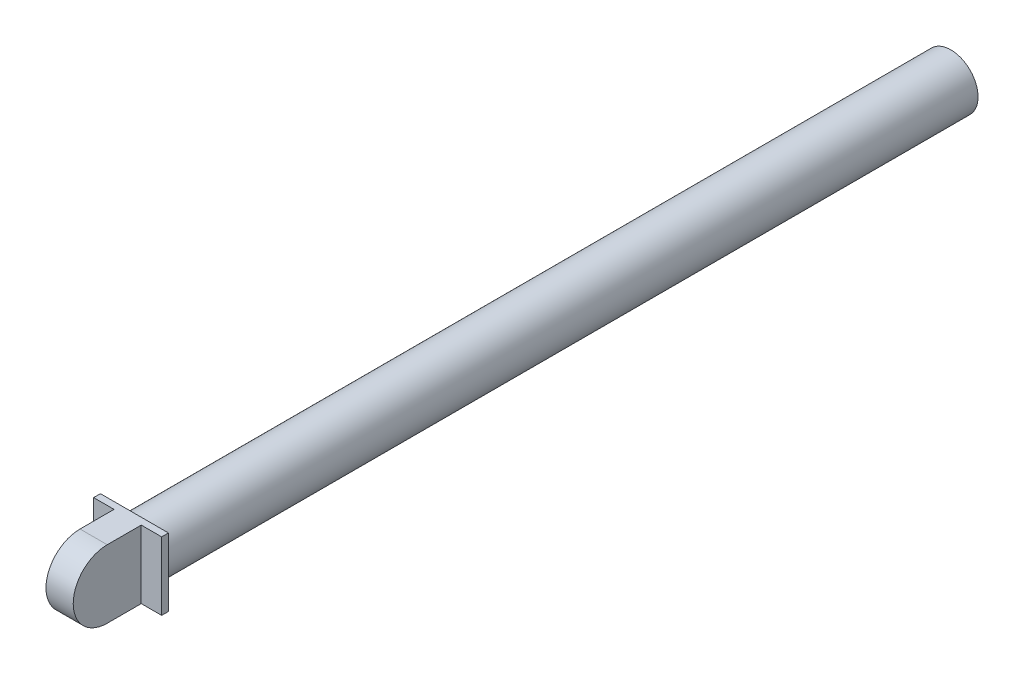
SolidWorks part; units mm, degrees
ref_plane "Front" through (0, 0, 0) normal (0, 0, 1) x (1, 0, 0)
ref_plane "Top" through (0, 0, 0) normal (0, 1, 0) x (1, 0, 0)
ref_plane "Right" through (0, 0, 0) normal (1, 0, 0) x (0, 0, -1)
sketch "草图1" plane through (0, 0, 0) normal (0, 0, 1) x (1, 0, 0)
  line L1 (-5, 5) -> (5, 5)
  line L2 (-5, 5) -> (-5, -5)
  line L3 (-5, -5) -> (5, -5)
  line L4 (5, 5) -> (5, -5)
  dimension "D1" = 10
  dimension "D2" = 10
  dimension "D3" = 5
  dimension "D4" = 5
extrude "凸台-拉伸1" add sketch "草图1" along normal blind 11
sketch "草图2" plane through (0, 5, 0) normal (0, 1, 0) x (1, 0, 0)
  line L0 (5, -11) -> (-5, -11) construction
  line L2 (-2, -11) -> (-2, -1)
  line L4 (2, -11) -> (2, -1)
  line L5 (0, 0) -> (0, -12.2093) construction
  line L6 (-5, -11) -> (-5, 0) construction
  line L7 (-5, -1) -> (-2, -1)
  line L8 (-5, -1) -> (-5, -11)
  line L9 (-5, -11) -> (-2, -11)
  line L10 (5, -1) -> (5, -11)
  line L11 (2, -11) -> (5, -11)
  line L12 (2, -1) -> (5, -1)
  dimension "D1" = 10
  dimension "D2" = 2
  dimension "D3" = 2
extrude "切除-拉伸1" cut sketch "草图2" against normal blind 11
sketch "草图3" plane through (0, 0, 0) normal (0, 0, -1) x (-1, 0, 0)
  circle A0 centre (0, 0) radius 4
extrude "凸台-拉伸2" add sketch "草图3" along normal blind 120
sketch "草图4" plane through (2, 0, 0) normal (1, 0, 0) x (0, 0, -1)
  line L1 (-6, 5) -> (-12.2957, 5)
  line L3 (-6, -5) -> (-12.2957, -5)
  line L4 (-12.2957, 5) -> (-12.2957, -5)
  arc A0 (-6, 5) -> (-6, -5) centre (-6, 0) ccw
extrude "切除-拉伸2" cut sketch "草图4" against normal blind 80
